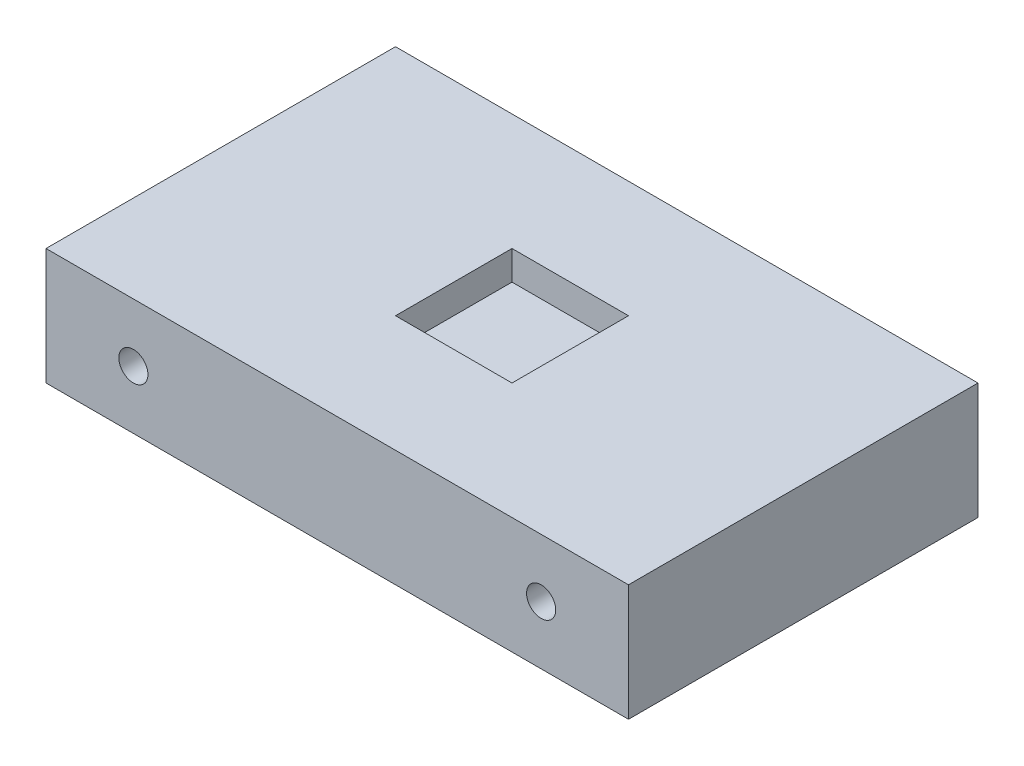
SolidWorks part; units mm, degrees
material "ASTM A36 Steel"
ref_plane "Front Plane" through (0, 0, 0) normal (0, 0, 1) x (1, 0, 0)
ref_plane "Top Plane" through (0, 0, 0) normal (0, 1, 0) x (1, 0, 0)
ref_plane "Right Plane" through (0, 0, 0) normal (1, 0, 0) x (0, 0, -1)
sketch "Sketch1" plane through (0, 0, 0) normal (0, 0, 1) x (1, 0, 0)
  line L1 (0, 0) -> (127, 0)
  line L2 (0, 0) -> (0, 25.4)
  line L3 (0, 25.4) -> (127, 25.4)
  line L4 (127, 0) -> (127, 25.4)
  dimension "D1" = 25.4
  dimension "D2" = 127
extrude "Boss-Extrude1" add sketch "Sketch1" along normal blind 76.2
sketch "Sketch2" plane through (0, 0, 76.2) normal (0, 0, 1) x (1, 0, 0)
  line L0 (0, 12.7) -> (127, 12.7) construction
  line L1 (0, 25.4) -> (0, 0) construction
  line L2 (127, 0) -> (127, 25.4) construction
  line L3 (19.05, 25.4) -> (19.05, 0) construction
  line L4 (127, 25.4) -> (0, 25.4) construction
  line L5 (0, 0) -> (127, 0) construction
  line L6 (107.95, 25.4) -> (107.95, 0) construction
  circle A0 centre (19.05, 12.7) radius 3.175
  circle A1 centre (107.95, 12.7) radius 3.175
  dimension "D3" = 6.35
  dimension "D4" = 6.35
  dimension "D1" = 19.05
  dimension "D2" = 19.05
extrude "Cut-Extrude1" cut sketch "Sketch2" against normal blind 12.7
sketch "Sketch3" plane through (0, 0, 0) normal (0, 0, -1) x (-1, 0, 0)
  line L0 (-127, 12.7) -> (0, 12.7) construction
  line L1 (-127, 0) -> (-127, 25.4) construction
  line L2 (0, 25.4) -> (0, 0) construction
  line L3 (-107.95, 25.4) -> (-107.95, 0) construction
  line L4 (-127, 25.4) -> (0, 25.4) construction
  line L5 (0, 0) -> (-127, 0) construction
  line L6 (-19.05, 25.4) -> (-19.05, 0) construction
  circle A0 centre (-107.95, 12.7) radius 3.175
  circle A1 centre (-19.05, 12.7) radius 3.175
  dimension "D3" = 6.35
  dimension "D4" = 6.35
  dimension "D1" = 19.05
  dimension "D2" = 19.05
extrude "Cut-Extrude2" cut sketch "Sketch3" against normal blind 12.7
sketch "Sketch4" plane through (0, 25.4, 0) normal (0, 1, 0) x (1, 0, 0)
  line L0 (127, 0) -> (0, 0) construction
  line L1 (50.8, -25.4) -> (76.2, -25.4)
  line L2 (50.8, -25.4) -> (50.8, -50.8)
  line L3 (50.8, -50.8) -> (76.2, -50.8)
  line L4 (76.2, -25.4) -> (76.2, -50.8)
  line L5 (127, -76.2) -> (0, -76.2) construction
  line L6 (127, -76.2) -> (127, 0) construction
  line L7 (0, -76.2) -> (0, 0) construction
  dimension "D1" = 25.4
  dimension "D2" = 25.4
  dimension "D3" = 50.8
  dimension "D4" = 50.8
extrude "Cut-Extrude3" cut sketch "Sketch4" against normal blind 6.35
